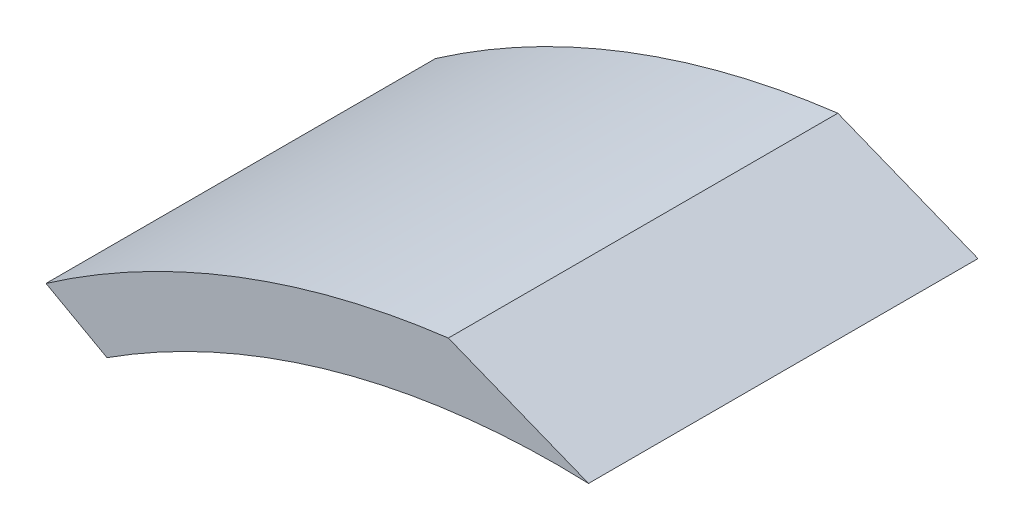
SolidWorks part; units mm, degrees
ref_plane "Front" through (0, 0, 0) normal (0, 0, 1) x (1, 0, 0)
ref_plane "Top" through (0, 0, 0) normal (0, 1, 0) x (1, 0, 0)
ref_plane "Right" through (0, 0, 0) normal (1, 0, 0) x (0, 0, -1)
sketch "Sketch1" plane through (0, 0, 0) normal (0, 0, 1) x (1, 0, 0)
  line L0 (0, 0) -> (0, -33.45)
  line L3 (-272.7937, -113.2968) -> (-292.569, -86.3183)
  arc A0 (0, 0) -> (-292.569, -86.3183) centre (-16.4657, -483.1695) ccw
  arc A2 (0, -33.45) -> (-272.7937, -113.2968) centre (-16.4554, -483.149) ccw
  dimension "D1" = 483.45
  dimension "D6" = 450
  dimension "D2" = 33.45
  dimension "D3" = 272.7937
  dimension "D4" = 33.45
  dimension "D5" = 292.569
  dimension "D7" = 79.8468
extrude "Boss-Extrude1" add sketch "Sketch1" along normal blind 210
sketch "Sketch3" plane through (0, 0, 0) normal (0, 0, -1) x (-1, 0, 0)
  line L0 (292.569, -86.3183) -> (255.4571, -106.8934)
  line L3 (-1450.932, -1052.9289) -> (274.3142, -96.4388) construction
  line L4 (255.4571, -106.8934) -> (272.7937, -113.2968)
  line L5 (272.7937, -113.2968) -> (292.569, -86.3183)
  dimension "D1" = 18.4814
extrude "Cut-Extrude1" cut sketch "Sketch3" against normal up to next
sketch "Sketch4" plane through (0, 0, 0) normal (0, 0, -1) x (-1, 0, 0)
  line L0 (0, -33.45) -> (84.0044, 0)
  line L1 (0, -33.45) -> (0, 0)
  line L2 (0, 0) -> (84.0044, 0)
  dimension "D1" = 84.0044
extrude "Cut-Extrude2" cut sketch "Sketch4" against normal up to next
